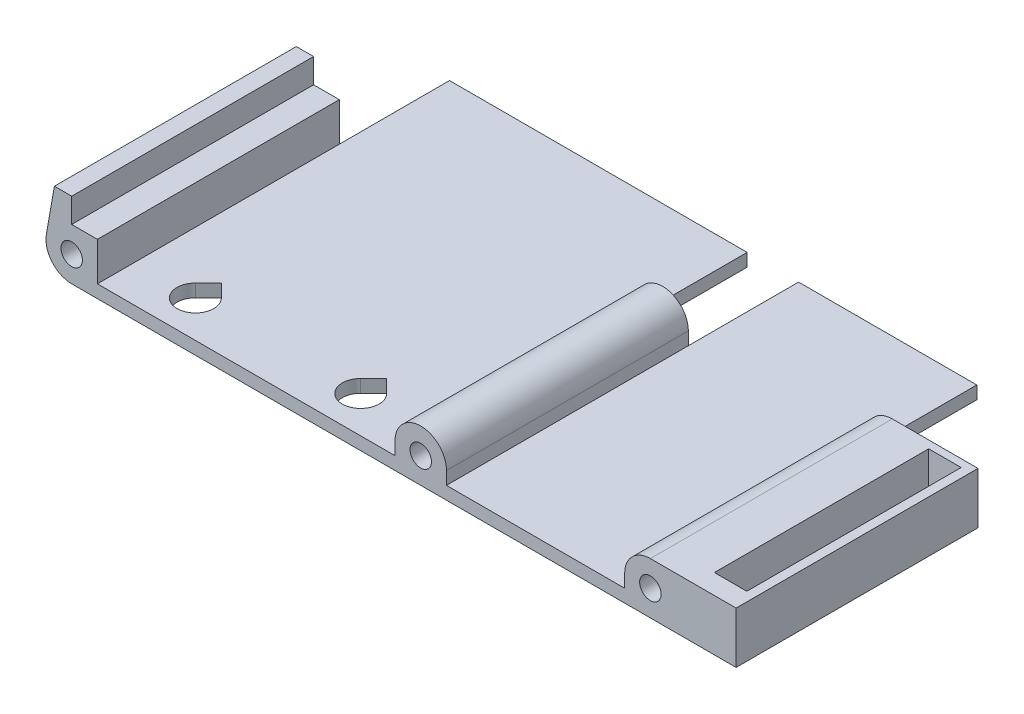
SolidWorks part; units mm, degrees
material "Custom Plastic"
ref_plane "Front Plane" through (0, 0, 0) normal (0, 0, 1) x (1, 0, 0)
ref_plane "Top Plane" through (0, 0, 0) normal (0, 1, 0) x (1, 0, 0)
ref_plane "Right Plane" through (0, 0, 0) normal (1, 0, 0) x (0, 0, -1)
sketch "Sketch1" plane through (0, 0, 0) normal (0, 0, 1) x (1, 0, 0)
  line L0 (-52.8, -2.1) -> (-4.2, -2.1)
  line L1 (-57, -4.2) -> (41.5, -4.2)
  line L2 (4.2, 0) -> (4.2, -2.1)
  line L3 (37.5, 4.2) -> (41.5, 4.2)
  line L4 (41.5, -4.2) -> (41.5, 4.2)
  line L5 (-4.2, 0) -> (-4.2, -2.1)
  line L6 (33.3, 0) -> (33.3, -2.1)
  line L7 (-52.8, 4.2) -> (-52.8, -2.1)
  line L8 (-57, 4.2) -> (-57, 8.2)
  line L9 (4.2, -2.1) -> (33.3, -2.1)
  line L10 (-57, 8.2) -> (-59.8189, 8.2)
  line L11 (-59.8189, 8.2) -> (-61.1362, 0.7293)
  line L12 (-57, 4.2) -> (-52.8, 4.2)
  circle A0 centre (0, 0) radius 1.75
  circle A1 centre (-57, 0) radius 1.75
  circle A2 centre (37.5, 0) radius 1.75
  arc A3 (-57, -4.2) -> (-61.1362, 0.7293) centre (-57, 0) cw
  arc A4 (37.5, 4.2) -> (33.3, 0) centre (37.5, 0) ccw
  arc A6 (4.2, 0) -> (-4.2, 0) centre (0, 0) ccw
  dimension "D2" = 37.5
  dimension "D3" = 3.5
  dimension "D1" = 57
  dimension "D4" = 4.2
  dimension "D5" = 4
  dimension "D6" = 2.1
  dimension "D7" = 10
  dimension "D8" = 4
extrude "Boss-Extrude1" add sketch "Sketch1" along normal blind 57.5
sketch "Sketch2" plane through (0, 4.2, 0) normal (0, 1, 0) x (1, 0, 0)
  line L0 (41.5, -57.5) -> (51.5, -57.5)
  line L1 (51.5, -57.5) -> (51.5, -17.5)
  line L2 (51.5, -17.5) -> (41.5, 0)
  line L3 (41.5, -57.5) -> (41.5, 0) construction
  line L4 (41.5, 0) -> (41.5, -57.5)
  dimension "D1" = 10
  dimension "D2" = 40
extrude "Boss-Extrude2" add sketch "Sketch2" against normal up to surface (8.4 mm away) up to face at (-7.75, -4.2, 28.75)
sketch "Sketch3" plane through (0, 4.2, 0) normal (0, 1, 0) x (1, 0, 0)
  line L0 (33.3, -57.5) -> (4.2, -57.5) construction
  line L1 (44.7, -54.25) -> (50, -54.25)
  line L2 (44.7, -54.25) -> (44.7, -19.25)
  line L3 (44.7, -19.25) -> (50, -19.25)
  line L4 (50, -54.25) -> (50, -19.25)
  dimension "D1" = 5.3
  dimension "D2" = 8.5
  dimension "D3" = 3.25
  dimension "D4" = 35
extrude "Cut-Extrude1" cut sketch "Sketch3" against normal offset from surface (5.4 mm away) 3 up to face at (6.1, -4.2, 26.5)
sketch "Sketch4" plane through (0, -2.1, 0) normal (0, 1, 0) x (1, 0, 0)
  line L1 (-45.8, -48.5) -> (-39.8, -48.5) construction
  line L2 (-45.8, -48.5) -> (-45.8, -54.5) construction
  line L3 (-45.8, -54.5) -> (-39.8, -54.5) construction
  line L4 (-39.8, -48.5) -> (-39.8, -54.5) construction
  line L6 (-4.2, -57.5) -> (-52.8, -57.5) construction
  line L7 (-44.9213, -49.3787) -> (-42.8, -47.2574)
  line L8 (-42.8, -47.2574) -> (-40.6787, -49.3787)
  line L9 (-52.8, -57.5) -> (-52.8, 0) construction
  arc A0 (-44.9213, -49.3787) -> (-40.6787, -49.3787) centre (-42.8, -51.5) ccw
  dimension "D1" = 6
  dimension "D2" = 6
  dimension "D3" = 3
  dimension "D4" = 10
extrude "Cut-Extrude2" cut sketch "Sketch4" against normal through all
sketch "Sketch5" plane through (0, 0, 0) normal (0, 0, -1) x (-1, 0, 0)
  line L0 (57, -4.2) -> (-41.5, -4.2) construction
  line L1 (-33.3, -4.2) -> (-51.5, -4.2)
  line L2 (-33.3, -4.2) -> (-33.3, 4.2)
  line L3 (-33.3, 4.2) -> (-51.5, 4.2)
  line L4 (-51.5, -4.2) -> (-51.5, 4.2)
  line L5 (57, 8.2) -> (59.8189, 8.2) construction
  line L6 (-4.2, -4.2) -> (4.2, -4.2)
  line L7 (-4.2, -4.2) -> (-4.2, 4.7374)
  line L8 (-4.2, 4.7374) -> (4.2, 4.7374)
  line L9 (4.2, -4.2) -> (4.2, 4.7374)
  line L10 (52.8, -4.2) -> (62.6756, -4.2)
  line L11 (52.8, -4.2) -> (52.8, 8.2)
  line L12 (52.8, 8.2) -> (62.6756, 8.2)
  line L13 (62.6756, -4.2) -> (62.6756, 8.2)
  line L14 (52.8, -2.1) -> (52.8, 4.2) construction
  line L15 (4.2, 0) -> (4.2, -2.1) construction
  line L16 (-4.2, -2.1) -> (-4.2, 0) construction
  line L17 (-33.3, 0) -> (-33.3, -2.1) construction
extrude "Cut-Extrude3" cut sketch "Sketch5" against normal blind 18
pattern_linear "LPattern1" count 2 spacing 27 along (1, 0, 0) of "Cut-Extrude2"
